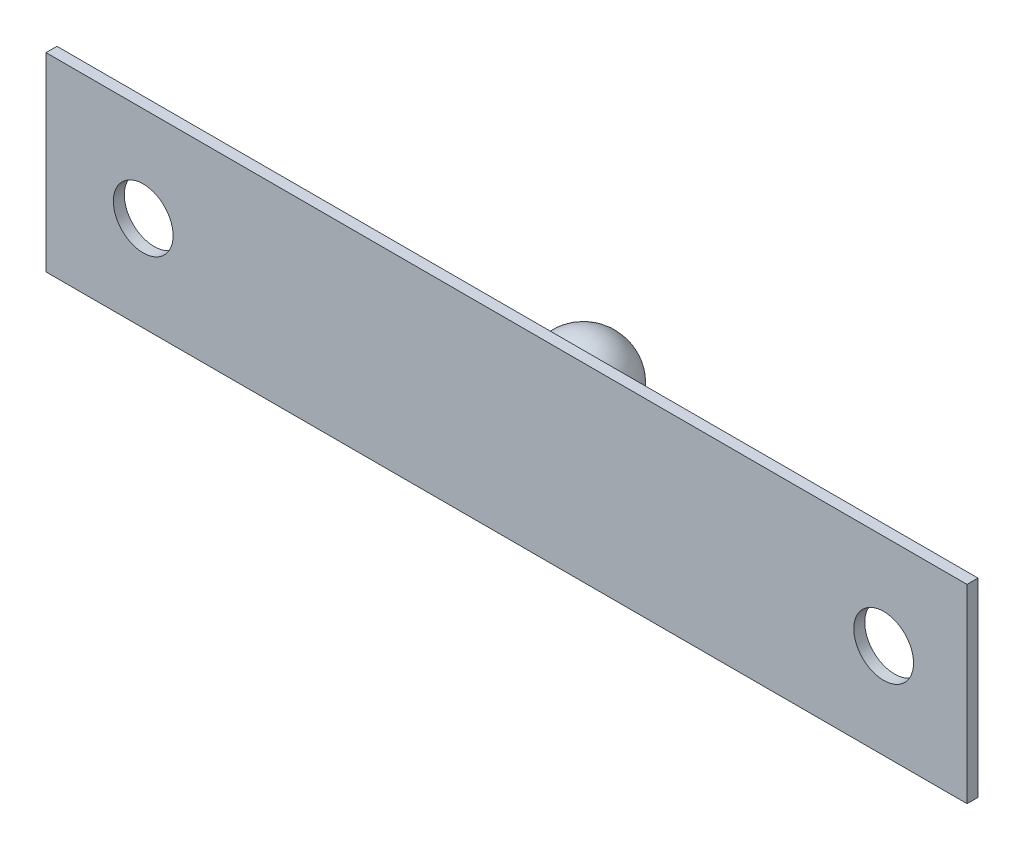
SolidWorks part; units mm, degrees
ref_plane "Front Plane" through (0, 0, 0) normal (0, 0, 1) x (1, 0, 0)
ref_plane "Top Plane" through (0, 0, 0) normal (0, 1, 0) x (1, 0, 0)
ref_plane "Right Plane" through (0, 0, 0) normal (1, 0, 0) x (0, 0, -1)
sketch "Sketch1" plane through (0, 0, 0) normal (0, 0, 1) x (1, 0, 0)
  line L1 (-18.5, -3.815) -> (18.5, -3.815)
  line L2 (-18.5, -3.815) -> (-18.5, 3.815)
  line L3 (-18.5, 3.815) -> (18.5, 3.815)
  line L4 (18.5, -3.815) -> (18.5, 3.815)
  line L5 (-18.5, -3.815) -> (18.5, 3.815) construction
  line L6 (-18.5, 3.815) -> (18.5, -3.815) construction
  circle A0 centre (-14.5941, 0) radius 1.2
  circle A1 centre (15.15, 0) radius 1.2
  point P0 (0, 0)
  point P10 (0, 0)
  point P11 (0, 0)
  dimension "D3" = 2.4
  dimension "D4" = 2.4
  dimension "D1" = 37
  dimension "D2" = 7.63
  dimension "D5" = 3.35
  dimension "D6" = 3.9059
extrude "Boss-Extrude1" add sketch "Sketch1" along normal blind 0.44
sketch "Sketch2" plane through (0, 0, 0) normal (0, 1, 0) x (1, 0, 0)
  line L0 (0, 0) -> (0, 4.42)
  line L1 (-1.525, 1.7367) -> (-1.525, 0)
  line L2 (18.5, 0) -> (-18.5, 0) construction
  line L3 (-1.525, 0) -> (0, 0)
  arc A0 (0, 4.42) -> (-1.525, 1.7367) centre (0, 2.645) ccw
  dimension "D2" = 3.55
  dimension "D1" = 4.42
  dimension "D3" = 1.525
revolve "Revolve2" add sketch "Sketch2" angle 360 about L0
